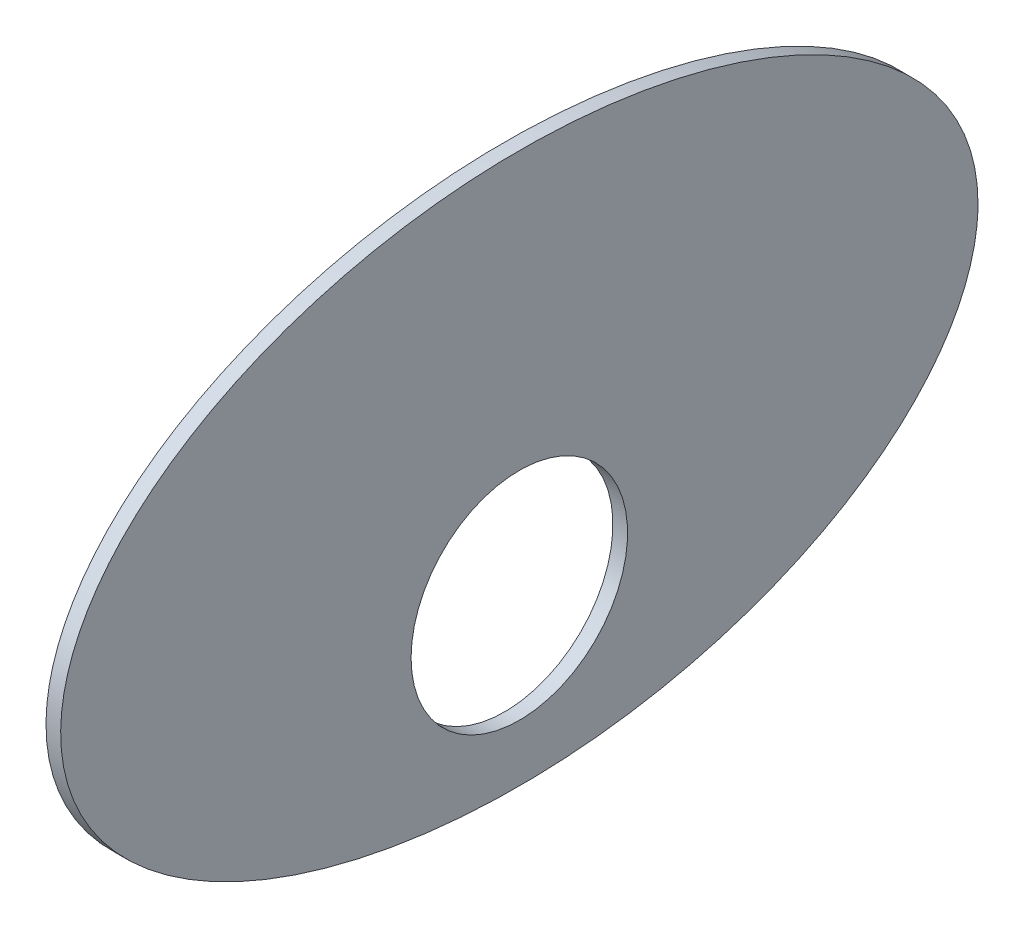
SolidWorks part; units mm, degrees
ref_plane "Front Plane" through (0, 0, 0) normal (0, 0, 1) x (1, 0, 0)
ref_plane "Top Plane" through (0, 0, 0) normal (0, 1, 0) x (1, 0, 0)
ref_plane "Right Plane" through (0, 0, 0) normal (1, 0, 0) x (0, 0, -1)
sketch "Sketch1" plane through (0, 0, 0) normal (1, 0, 0) x (0, 0, -1)
  ellipse E0 centre (0, 0) end of major axis (125, 0) minor radius 75
  dimension "D1" = 250
  dimension "D2" = 150
extrude "Boss-Extrude1" add sketch "Sketch1" along normal blind 4
sketch "Sketch2" plane through (0, 0, 0) normal (-1, 0, 0) x (0, 0, 1)
  circle A2 centre (0, -30) radius 29.5
  dimension "D1" = 59
  dimension "D4" = 30
extrude "Cut-Extrude1" cut sketch "Sketch2" against normal through all
